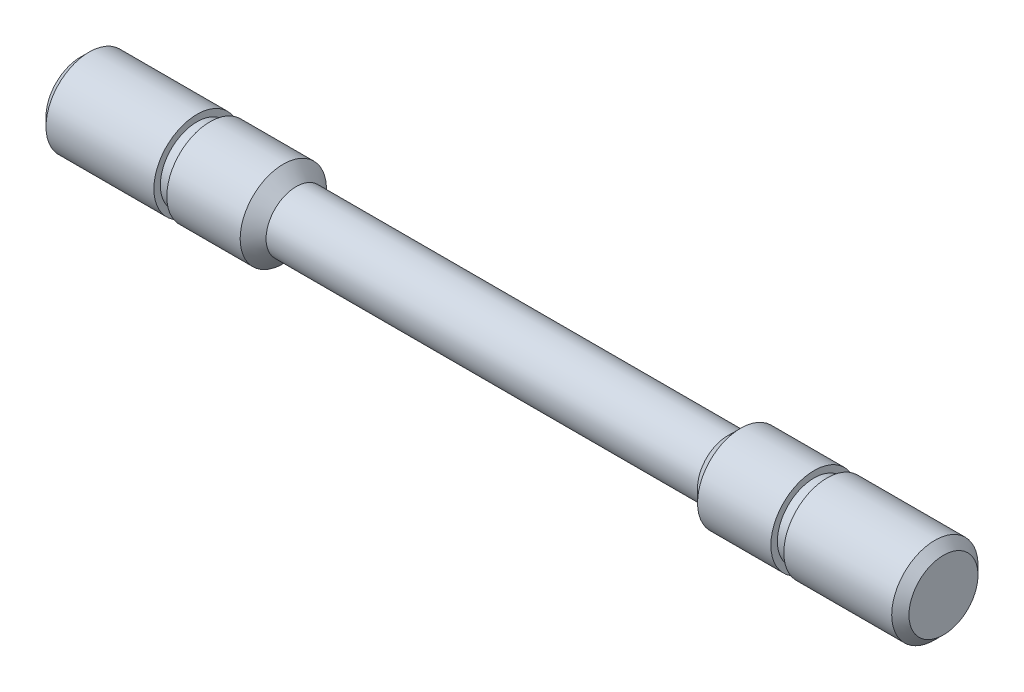
SolidWorks part; units mm, degrees
material "XC38"
ref_plane "Face" through (0, 0, 0) normal (0, 0, 1) x (1, 0, 0)
ref_plane "Dessus" through (0, 0, 0) normal (0, 1, 0) x (1, 0, 0)
ref_plane "Droite" through (0, 0, 0) normal (1, 0, 0) x (0, 0, -1)
sketch "Esquisse1" plane through (0, 0, 0) normal (0, 0, 1) x (1, 0, 0)
  line L0 (0, 0) -> (0, 3.5)
  line L1 (0, 3.5) -> (-25, 3.5)
  line L2 (-25, 3.5) -> (-26.5, 5)
  line L3 (-26.5, 5) -> (-35, 5)
  line L4 (-35, 5) -> (-35, 4.25)
  line L5 (-35, 4.25) -> (-36.5, 4.25)
  line L6 (-36.5, 4.25) -> (-36.5, 5)
  line L7 (-50, 0) -> (0, 0)
  line L8 (-36.5, 5) -> (-49, 5)
  line L9 (-50, 4) -> (-50, 0)
  line L10 (-49, 5) -> (-50, 4)
  point P11 (-50, 5)
  dimension "D1" = 3.5
  dimension "D2" = 5
  dimension "D3" = 45
  dimension "D4" = 25
  dimension "D5" = 8.5
  dimension "D6" = 4.25
  dimension "D7" = 23.5
  dimension "D8" = 1.5
revolve "Révolution1" add sketch "Esquisse1" angle 360 about L7
cosmetic thread "Représentation de filetage1" parameters "D2"=6.619
mirror "Symétrie1" of "Révolution1"
